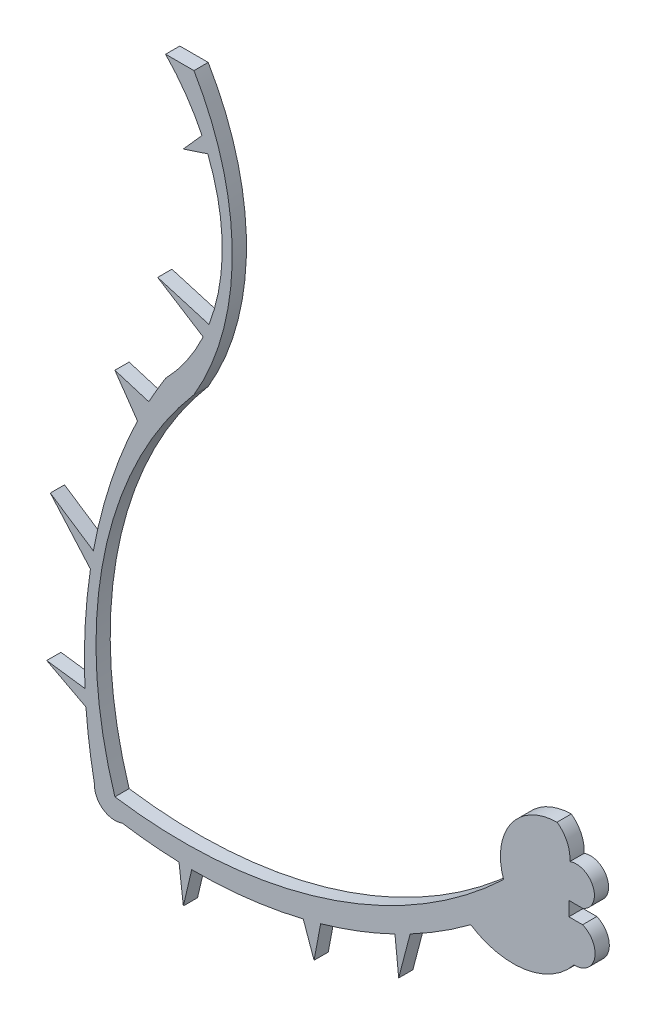
SolidWorks part; units mm, degrees
ref_plane "Front Plane" through (0, 0, 0) normal (0, 0, 1) x (1, 0, 0)
ref_plane "Top Plane" through (0, 0, 0) normal (0, 1, 0) x (1, 0, 0)
ref_plane "Right Plane" through (0, 0, 0) normal (1, 0, 0) x (0, 0, -1)
sketch "Sketch1" plane through (0, 0, 0) normal (0, 0, 1) x (1, 0, 0)
  line L0 (-9.4455, 0) -> (-9.4455, -1.524)
  line L1 (-9.4455, -1.524) -> (-6.7075, -1.524)
  line L2 (-51.3895, 56.9103) -> (-48.3484, 56.9103)
  line L4 (-6.7075, 0) -> (-8.1803, 0)
  line L5 (-8.1803, 0) -> (-8.1803, -1.524)
  line L6 (-8.1803, -1.524) -> (-6.7075, -1.524)
  line L7 (-25.1859, -11.6191) -> (-26.4167, -16.3225)
  line L8 (-26.4167, -16.3225) -> (-26.8127, -12.4402)
  line L9 (-36.6403, -15.9568) -> (-35.4828, -19.2128)
  line L10 (-35.4828, -19.2128) -> (-34.7764, -15.4656)
  line L11 (-48.5916, -17.3575) -> (-49.4884, -21.1745)
  line L12 (-49.4884, -21.1745) -> (-49.9519, -17.3322)
  line L13 (-59.9249, -7.9302) -> (-64.1279, -5.717)
  line L14 (-64.1279, -5.717) -> (-60.0289, -6.269)
  line L15 (-59.4418, 5.1072) -> (-63.7415, 10.0168)
  line L16 (-63.7415, 10.0168) -> (-59.1298, 6.9521)
  line L17 (-54.4011, 21.3777) -> (-56.8223, 24.8687)
  line L18 (-56.8223, 24.8687) -> (-53.1806, 23.7624)
  line L19 (-47.3635, 32.688) -> (-52.2382, 35.7753)
  line L20 (-52.2382, 35.7753) -> (-46.7402, 34.1577)
  line L21 (-46.8711, 49.9244) -> (-49.4884, 49.0659)
  line L22 (-49.4884, 49.0659) -> (-47.487, 51.3185)
  arc A0 (-6.7075, -1.524) -> (-7.6314, -5.717) centre (-7.5532, -3.536) cw
  arc A1 (-7.6314, -5.717) -> (-18.6956, -7.5211) centre (-14.1622, -0.4943) cw
  arc A2 (-18.6956, -7.5211) -> (-25.1859, -11.6191) centre (-48.3484, 32.2531) cw
  arc A3 (-56.0343, -16.7592) -> (-59.0096, -14.6165) centre (-56.8223, -14.7163) cw
  arc A4 (-59.0096, -14.6165) -> (-59.9249, -7.9302) centre (-2.8186, -3.5186) cw
  arc A5 (-51.3895, 26.8369) -> (-47.3635, 32.688) centre (-66.9779, 41.8736) ccw
  arc A6 (-48.3484, 56.9103) -> (-48.3484, 26.8369) centre (-73.8614, 41.8736) cw
  arc A7 (-48.3484, 26.8369) -> (-56.8223, -14.7163) centre (-15.1745, -1.5688) ccw
  arc A8 (-56.8223, -14.7163) -> (-15.1745, -1.5688) centre (-49.4884, 34.5903) ccw
  arc A9 (-15.1745, -1.5688) -> (-9.4455, 6.6243) centre (-9.3427, 0.4528) cw
  arc A10 (-9.4455, 6.6243) -> (-8.0765, 3.6516) centre (-11.3877, 3.9282) cw
  arc A11 (-8.0765, 3.6516) -> (-6.7075, 0) centre (-7.392, 1.8258) cw
  arc A12 (-47.487, 51.3185) -> (-51.3895, 56.9103) centre (-66.9779, 41.8736) ccw
  arc A13 (-46.7402, 34.1577) -> (-46.8711, 49.9244) centre (-66.9779, 41.8736) ccw
  arc A14 (-53.1806, 23.7624) -> (-51.3895, 26.8369) centre (-2.8186, -3.5186) cw
  arc A15 (-59.1298, 6.9521) -> (-54.4011, 21.3777) centre (-2.8186, -3.5186) cw
  arc A16 (-60.0289, -6.269) -> (-59.4418, 5.1072) centre (-2.8186, -3.5186) cw
  arc A17 (-49.9519, -17.3322) -> (-56.0343, -16.7592) centre (-48.3484, 32.2531) cw
  arc A18 (-36.6403, -15.9568) -> (-48.5916, -17.3575) centre (-48.3484, 32.2531) cw
  arc A19 (-26.8127, -12.4402) -> (-34.7764, -15.4656) centre (-48.3484, 32.2531) cw
extrude "Boss-Extrude1" add sketch "Sketch1" along normal blind 1.524
